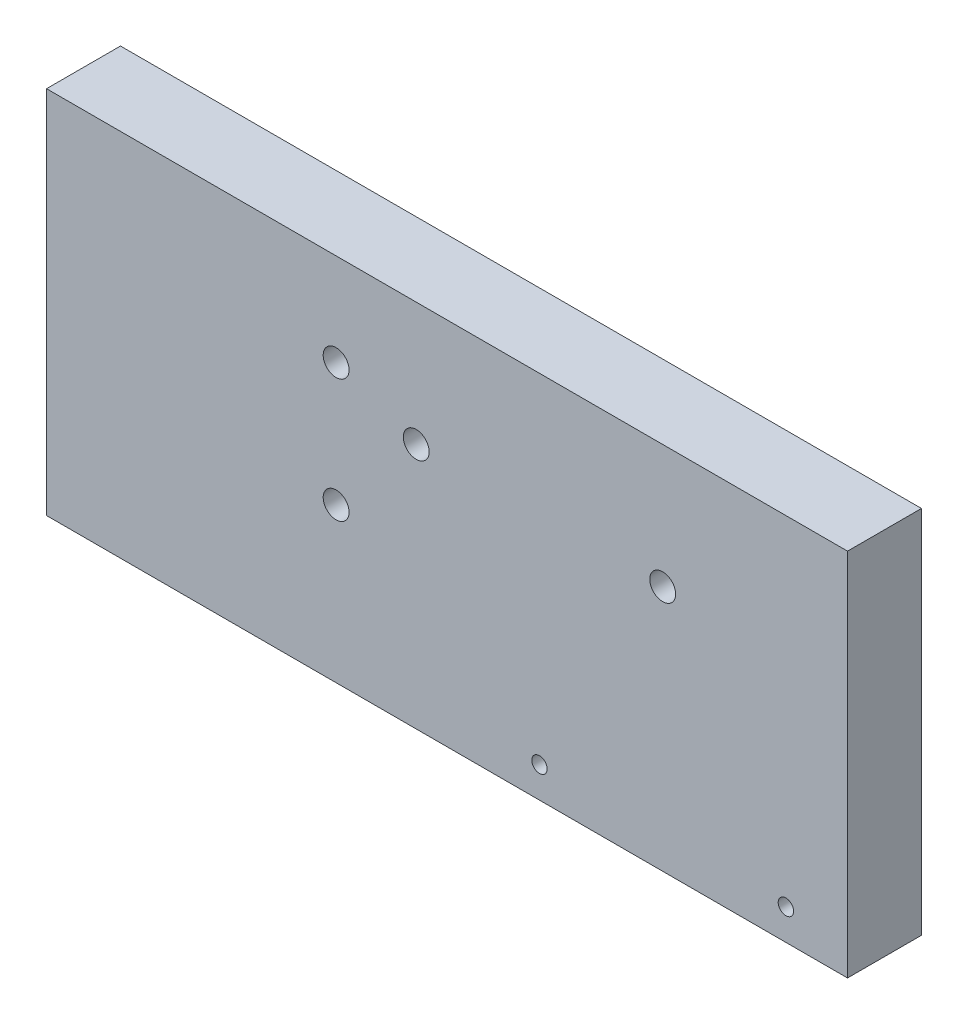
SolidWorks part; units mm, degrees
ref_plane "Front Plane" through (0, 0, 0) normal (0, 0, 1) x (1, 0, 0)
ref_plane "Top Plane" through (0, 0, 0) normal (0, 1, 0) x (1, 0, 0)
ref_plane "Right Plane" through (0, 0, 0) normal (1, 0, 0) x (0, 0, -1)
sketch "Sketch1" plane through (0, 0, 0) normal (0, 0, 1) x (1, 0, 0)
  line L5 (-65, -30) -> (65, -30)
  line L6 (-65, -30) -> (-65, 30)
  line L7 (-65, 30) -> (65, 30)
  line L8 (65, -30) -> (65, 30)
  line L9 (-65, -30) -> (65, 30) construction
  line L10 (-65, 30) -> (65, -30) construction
  point P0 (0, 0)
  dimension "D1" = 130
  dimension "D2" = 60
extrude "Boss-Extrude1" add sketch "Sketch1" along normal mid plane 12
hole_wizard "M5x0.8 Tapped Hole1" positions "Sketch3" profile "Sketch4" tap size "M5x0.8" standard "ANSI Metric" end condition through all
sketch "Sketch3" plane through (0, 0, 6) normal (0, 0, 1) x (1, 0, 0)
  line L0 (65, 30) -> (-65, 30) construction
  line L1 (-65, 30) -> (-65, -30) construction
  line L2 (65, -30) -> (65, 30) construction
  point P0 (-18, 15)
  point P2 (-18, -5)
  point P4 (-5, 10)
  point P6 (35, 10)
  point P15 (0, 0)
  dimension "D1" = 15
  dimension "D2" = 20
  dimension "D3" = 47
  dimension "D4" = 40
  dimension "D5" = 30
  dimension "D6" = 20
sketch "Sketch4" plane through (-18, 15, 6) normal (1, 0, 0) x (0, -1, 0)
  line L0 (0, 0) -> (0, 12)
  line L1 (0, 12) -> (2.1, 12)
  line L2 (2.1, 12) -> (2.1, 0)
  line L5 (2.1, 0) -> (0, 0)
  line L11 (0, -6.35) -> (0, 107.95) construction
  dimension "Thru Tap Drill Dia." = 4.2
  dimension "Thru Tap Drill Depth" = 12
cosmetic thread "Hole Thread1"
cosmetic thread "Hole Thread2"
cosmetic thread "Hole Thread3"
cosmetic thread "Hole Thread4"
hole_wizard "M3x0.5 Tapped Hole1" positions "Sketch5" profile "Sketch6" tap size "M3x0.5" standard "ANSI Metric" end condition through all
sketch "Sketch5" plane through (0, 0, 6) normal (0, 0, 1) x (1, 0, 0)
  line L0 (-65, -30) -> (65, -30) construction
  line L1 (65, -30) -> (65, 30) construction
  point P0 (15, -25)
  point P2 (55, -25)
  point P9 (0, 0)
  dimension "D1" = 5
  dimension "D2" = 10
  dimension "D3" = 40
sketch "Sketch6" plane through (15, -25, 6) normal (1, 0, 0) x (0, -1, 0)
  line L0 (0, 0) -> (0, 12)
  line L1 (0, 12) -> (1.25, 12)
  line L2 (1.25, 12) -> (1.25, 0)
  line L5 (1.25, 0) -> (0, 0)
  line L11 (0, -6.35) -> (0, 107.95) construction
  dimension "Thru Tap Drill Dia." = 2.5
  dimension "Thru Tap Drill Depth" = 12
cosmetic thread "Hole Thread5"
cosmetic thread "Hole Thread6"
